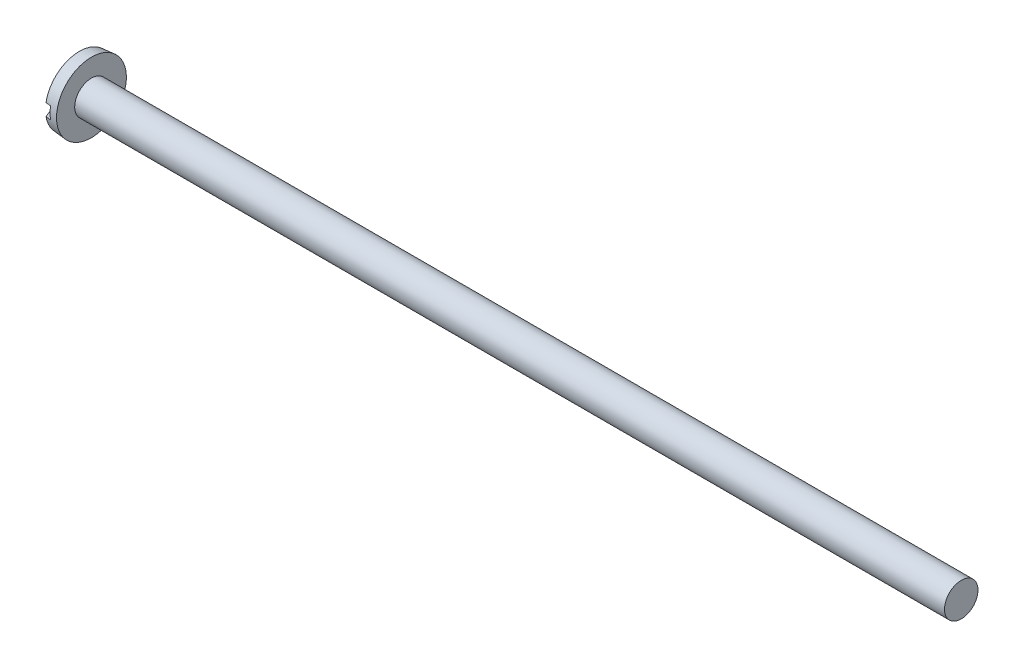
SolidWorks part; units mm, degrees
ref_plane "Plane1" through (0, 0, 0) normal (0, 0, 1) x (1, 0, 0)
ref_plane "Plane2" through (0, 0, 0) normal (0, 1, 0) x (1, 0, 0)
ref_plane "Plane3" through (0, 0, 0) normal (1, 0, 0) x (0, 0, -1)
other "Configuration Table"
sketch "BodySke" plane through (0, 0, 0) normal (0, 0, 1) x (1, 0, 0)
  line L0 (0.7112, 0.5969) -> (0.7112, 1.2446)
  line L1 (0.7112, 1.2446) -> (0.2794, 1.2068)
  line L2 (-25.4, 0) -> (127, 0) construction
  line L3 (0.7112, -1.2446) -> (0.2794, -1.2068) construction
  line L4 (0.7112, 0.5969) -> (16.5862, 0.5969)
  line L5 (16.5862, 0.5969) -> (16.5862, 0)
  line L6 (16.5862, 0) -> (0, 0)
  line L7 (0.7112, -0.5969) -> (16.5862, -0.5969) construction
  line L8 (0.9754, 6.35) -> (0.9754, -3.175) construction
  line L9 (0.7112, 6.35) -> (0.7112, -3.175) construction
  arc A0 (0, 0) -> (0.2794, 1.2068) centre (2.746, 0) cw
  dimension "Head_ang" = 85
  dimension "Oval_ht" = 0.2794
  dimension "Head_ht" = 0.7112
  dimension "Diameter" = 1.1938
  dimension "Length" = 15.875
  dimension "Head_dia" = 2.4892
  dimension "Advance" = 0.2642
  dimension "Thread_nom" = 15.875
revolve "Base-Revolve" add sketch "BodySke" angle 360 about L2
cosmetic thread "ThreadCosmetic" [suppressed] parameters "Thread_length"=15.6108, "Thread_minor"=0.8484
sketch "Sketch2" plane through (0, 0, 0) normal (1, 0, 0) x (0, 0, -1)
  line L0 (1.2446, -0.2159) -> (1.2446, 0.2159)
  line L1 (1.2446, 0.2159) -> (-1.2446, 0.2159)
  line L2 (-1.2446, 0.2159) -> (-1.2446, -0.2159)
  line L3 (-1.2446, -0.2159) -> (1.2446, -0.2159)
  dimension "D1" = 2.4892
  dimension "D2" = 1.2446
  dimension "D3" = 0.2159
  dimension "Slot_width" = 0.4318
extrude "Slot" cut sketch "Sketch2" along normal blind 0.4572
sketch "Sketch3" plane through (0, 0, 0) normal (1, 0, 0) x (0, 0, -1)
  line L0 (-0.127, 0.508) -> (0.127, 0.508)
  line L1 (0.127, 0.508) -> (0.127, -0.508)
  line L2 (0.127, -0.508) -> (-0.127, -0.508)
  line L3 (-0.127, -0.508) -> (-0.127, 0.508)
  dimension "Cross_width" = 0.254
  dimension "D1" = 0.127
  dimension "Cross_dia" = 1.016
  dimension "D2" = 0.508
ref_plane "Plane4" through (0.508, 0, 0) normal (1, 0, 0) x (0, 0, -1)
sketch "Sketch4" plane through (0.508, 0, 0) normal (1, 0, 0) x (0, 0, -1)
  line L0 (-0.0635, 0.0635) -> (0.0635, 0.0635)
  line L1 (0.0635, 0.0635) -> (0.0635, -0.0635)
  line L2 (0.0635, -0.0635) -> (-0.0635, -0.0635)
  line L3 (-0.0635, -0.0635) -> (-0.0635, 0.0635)
  dimension "D1" = 0.127
  dimension "D2" = 0.0635
  dimension "D3" = 0.127
  dimension "D4" = 0.0635
loft "Cross" [suppressed] cut profiles "Sketch3", "Sketch4"
pattern_circular "CirPattern1" [suppressed] count 2 every 90 about axis through (-25.4, 0, 0) along (1, 0, 0)
sketch "ThdSchSke" plane through (0, 0, 0) normal (0, 0, 1) x (1, 0, 0)
  line L0 (0.9754, -0.4242) -> (0.8544, -0.5969)
  line L1 (0.9754, -0.4242) -> (1.0963, -0.5969)
  line L2 (1.0963, -0.5969) -> (1.0963, -0.7461)
  line L3 (-3.175, 0) -> (5.1513, 0) construction
  line L5 (1.0963, -0.7461) -> (0.8544, -0.7461)
  line L6 (0.8544, -0.7461) -> (0.8544, -0.5969)
  dimension "Diameter" = 1.1938
  dimension "SideAngle" = 55
  dimension "VeeAngle" = 70
  dimension "Thread_minor" = 0.8484
  dimension "Overcut" = 1.4922
  dimension "Start" = 0.9754
revolve "ThreadSchematic" [suppressed] cut sketch "ThdSchSke" angle 360 about L3
pattern_linear "ThdSchPat" [suppressed]
sketch "Schizzo2" plane through (16.5862, 0, 0) normal (1, 0, 0) x (0, 0, -1)
  circle A0 centre (0, 0) radius 0.5969
  dimension "D1" = 1.1938
extrude "Estrusione-Estrusione1" add sketch "Schizzo2" along normal blind 15.1257
equation "\"D1@Sketch3\" = \"Cross_width@Sketch3\" / 2"
equation "\"D2@Sketch3\" = \"Cross_dia@Sketch3\" / 2"
equation "\"D1@Sketch4\" = \"Cross_width@Sketch3\"*.5"
equation "\"D2@Sketch4\" = \"D1@Sketch4\" / 2"
equation "\"D3@Sketch4\" = \"D1@Sketch4\""
equation "\"D4@Sketch4\" = \"D2@Sketch4\""
equation "\"D1@Sketch2\" = \"Head_dia@BodySke\""
equation "\"D2@Sketch2\" = \"D1@Sketch2\" / 2"
equation "\"D3@Sketch2\" = \"Slot_width@Sketch2\" / 2"
equation "\"Thread_length@ThreadCosmetic\" = ((sgn( (\"Length@BodySke\" - \"Advance@BodySke\" ) - \"Thread_nom@BodySke\" )-1)*( (\"Length@BodySke\" - \"Advance@BodySke\" ) - \"Thread_nom@BodySke\" ))/-2+ \"Thread_nom@BodySke\""
equation "\"Thread_minor@ThdSchSke\" = \"Thread_minor@ThreadCosmetic\""
equation "\"Diameter@ThdSchSke\" = \"Diameter@BodySke\""
equation "\"Overcut@ThdSchSke\" = \"Diameter@BodySke\" * 1.25"
equation "\"Start@ThdSchSke\" = \"Head_ht@BodySke\" + \"Length@BodySke\" - \"Thread_length@ThreadCosmetic\"  '---Non-countersunk---"
equation "\"Num_threads@ThdSchPat\" = int( \"Thread_length@ThreadCosmetic\" / \"Advance@BodySke\" + 0.999 )  + 1"
equation "\"Advance@ThdSchPat\" = \"Thread_length@ThreadCosmetic\" /  (\"Num_threads@ThdSchPat\" - 1) 'relax it"
